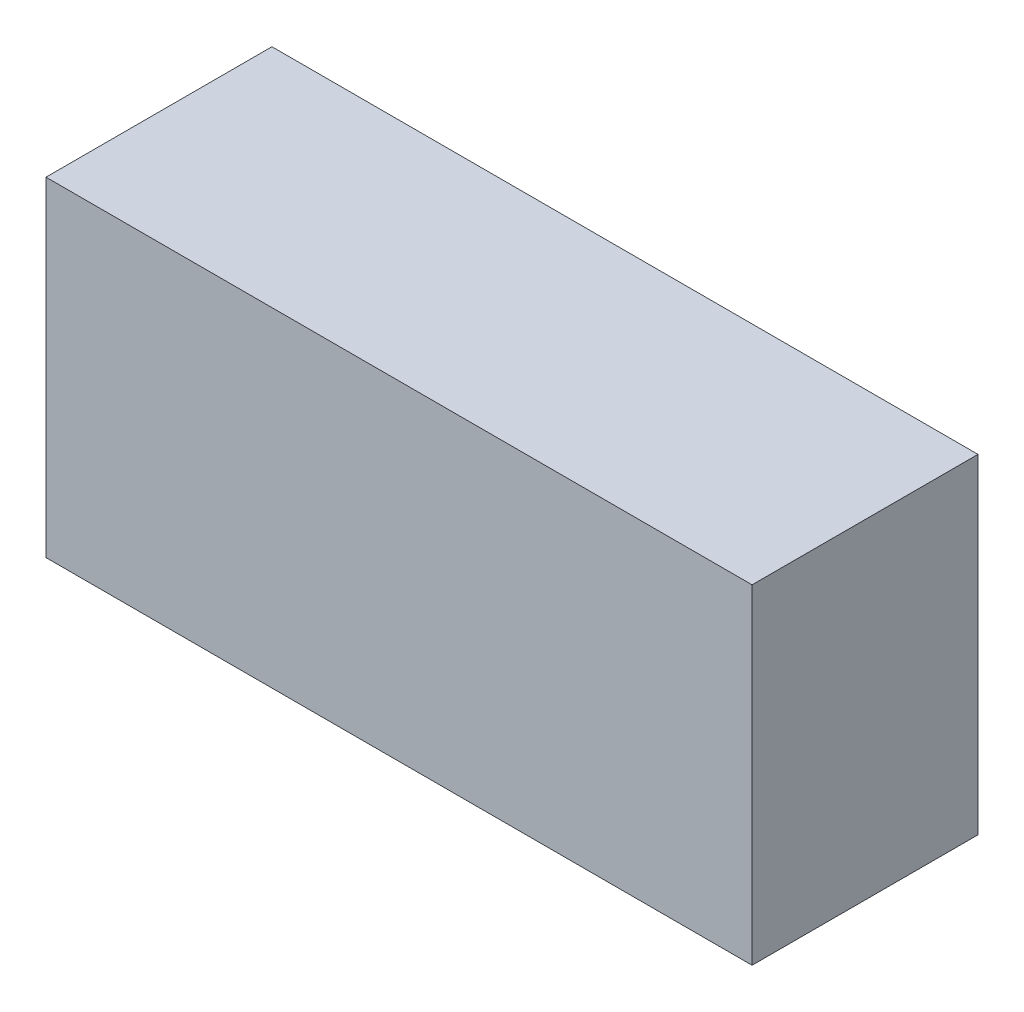
SolidWorks part; units mm, degrees
ref_plane "Front Plane" through (0, 0, 0) normal (0, 0, 1) x (1, 0, 0)
ref_plane "Top Plane" through (0, 0, 0) normal (0, 1, 0) x (1, 0, 0)
ref_plane "Right Plane" through (0, 0, 0) normal (1, 0, 0) x (0, 0, -1)
sketch "Sketch1" plane through (0, 0, 0) normal (0, 0, 1) x (1, 0, 0)
  line L5 (0, 0) -> (75, 0)
  line L6 (0, 0) -> (0, 35)
  line L7 (0, 35) -> (75, 35)
  line L8 (75, 0) -> (75, 35)
  point P4 (0, 0)
  dimension "D1" = 35
  dimension "D2" = 75
extrude "Boss-Extrude1" add sketch "Sketch1" along normal blind 24
